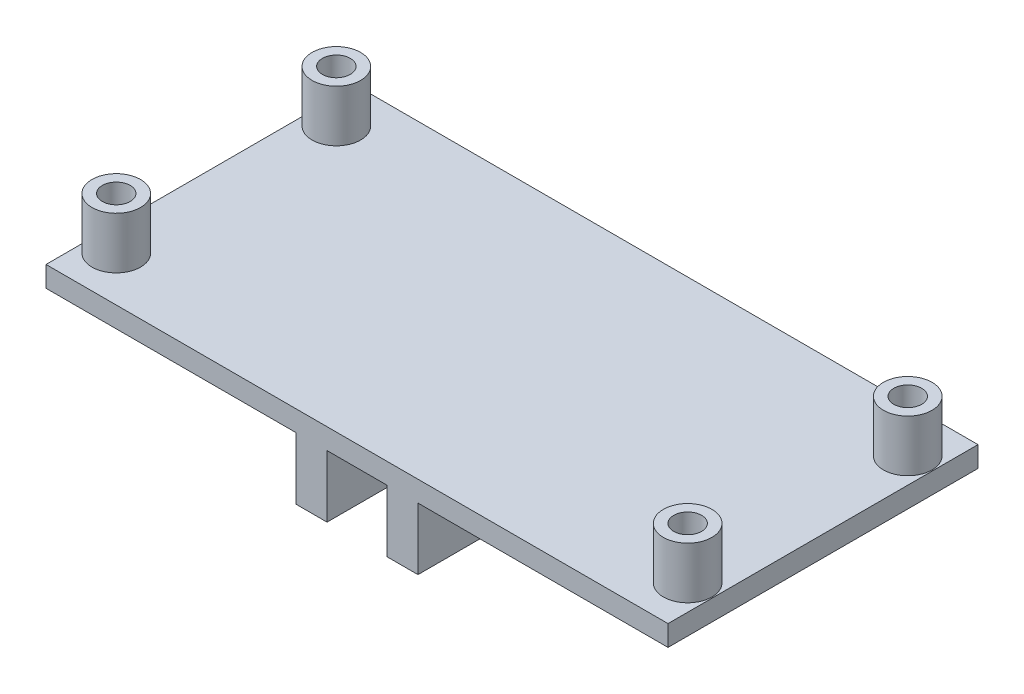
SolidWorks part; units mm, degrees
ref_plane "前视基准面" through (0, 0, 0) normal (0, 0, 1) x (1, 0, 0)
ref_plane "上视基准面" through (0, 0, 0) normal (0, 1, 0) x (1, 0, 0)
ref_plane "右视基准面" through (0, 0, 0) normal (1, 0, 0) x (0, 0, -1)
sketch "草图1" plane through (0, 0, 0) normal (0, 1, 0) x (1, 0, 0)
  line L1 (-30.1, 15) -> (30.1, 15)
  line L2 (-30.1, 15) -> (-30.1, -15)
  line L3 (-30.1, -15) -> (30.1, -15)
  line L4 (30.1, 15) -> (30.1, -15)
  line L5 (-30.1, 15) -> (30.1, -15) construction
  line L6 (-30.1, -15) -> (30.1, 15) construction
  point P0 (0, 0)
  dimension "D1" = 60.2
  dimension "D2" = 30
extrude "凸台-拉伸1" add sketch "草图1" along normal blind 2
sketch "草图2" plane through (0, 2, 0) normal (0, 1, 0) x (1, 0, 0)
  line L0 (0, 24.2514) -> (0, -24.8586) construction
  line L1 (-35.6866, 0) -> (41.7265, 0) construction
  circle A0 centre (-27.65, 10.65) radius 1.35
  circle A1 centre (-27.65, -10.65) radius 1.35
  circle A2 centre (27.65, -10.65) radius 1.35
  circle A3 centre (27.65, 10.65) radius 1.35
  dimension "D1" = 27.65
  dimension "D2" = 10.65
extrude "切除-拉伸1" cut sketch "草图2" against normal through all
sketch "草图3" plane through (0, 2, 0) normal (0, 1, 0) x (1, 0, 0)
  circle A0 centre (27.65, 10.65) radius 1.35
  circle A1 centre (27.65, -10.65) radius 1.35
  circle A2 centre (-27.65, -10.65) radius 1.35
  circle A3 centre (-27.65, 10.65) radius 1.35
  circle A5 centre (-27.65, 10.65) radius 2.35
  circle A6 centre (27.65, 10.65) radius 2.35
  circle A7 centre (27.65, -10.65) radius 2.35
  circle A8 centre (-27.65, -10.65) radius 2.35
  dimension "D1" = 1
extrude "凸台-拉伸2" add sketch "草图3" along normal blind 5
sketch "草图4" plane through (0, 0, 0) normal (0, -1, 0) x (1, 0, 0)
  line L0 (0, -21.4578) -> (0, 24.343) construction
  line L1 (30.1, -15) -> (-30.1, -15) construction
  line L2 (5.9, -15) -> (2.9, -15)
  line L3 (5.9, -15) -> (5.9, 15)
  line L4 (5.9, 15) -> (2.9, 15)
  line L5 (2.9, -15) -> (2.9, 15)
  line L6 (-30.1, 15) -> (30.1, 15) construction
  line L7 (-5.9, 15) -> (-2.9, 15)
  line L8 (-5.9, -15) -> (-5.9, 15)
  line L9 (-5.9, -15) -> (-2.9, -15)
  line L10 (-2.9, -15) -> (-2.9, 15)
  dimension "D1" = 2.9
  dimension "D2" = 3
extrude "凸台-拉伸3" add sketch "草图4" along normal blind 6
sketch "草图5" plane through (-5.9, 0, 0) normal (-1, 0, 0) x (0, 0, 1)
  line L0 (0, -3.1046) -> (0, 13.8776) construction
  line L1 (-15, 0) -> (15, 0) construction
  circle A0 centre (-7, -3.75) radius 1.5
  circle A1 centre (7.35, -3.75) radius 1.5
  dimension "D1" = 3.75
  dimension "D2" = 14.35
  dimension "D3" = 7
extrude "切除-拉伸2" cut sketch "草图5" against normal through all
